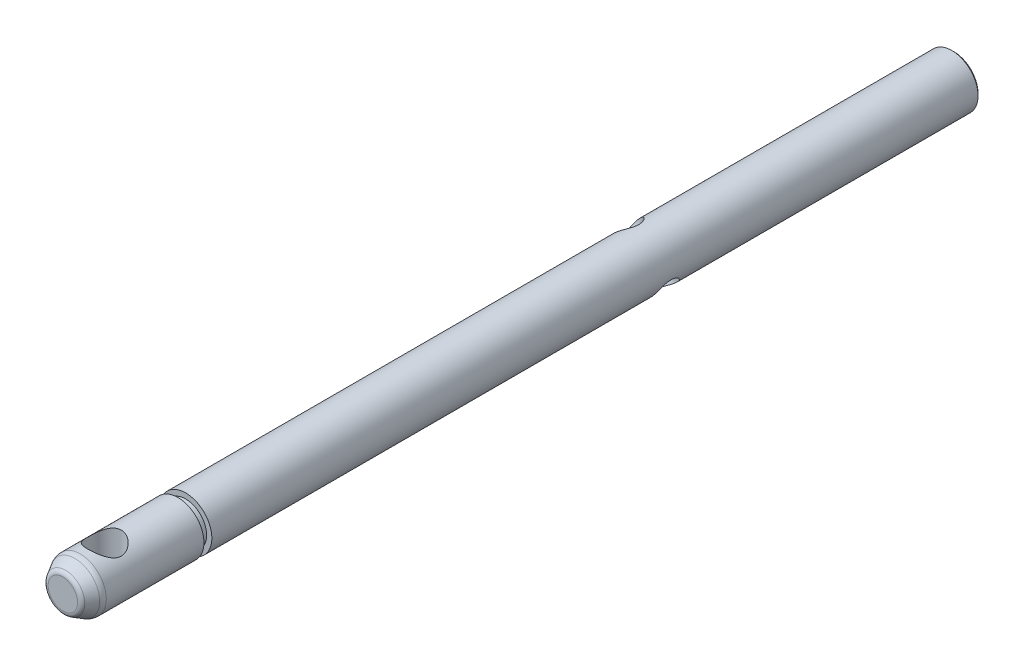
SolidWorks part; units mm, degrees
material "AISI Type 316L stainless steel"
ref_plane "Front Plane" through (0, 0, 0) normal (0, 0, 1) x (1, 0, 0)
ref_plane "Top Plane" through (0, 0, 0) normal (0, 1, 0) x (1, 0, 0)
ref_plane "Right Plane" through (0, 0, 0) normal (1, 0, 0) x (0, 0, -1)
ref_plane "Plane1" through (0, 0, 0) normal (0, -1, 0) x (1, 0, 0)
sketch "Sketch1" plane through (0, 0, 0) normal (0, -1, 0) x (1, 0, 0)
  line L0 (1.7, 11.75) -> (0, 11.75)
  line L1 (0, 11.75) -> (0, -73.5)
  line L2 (0, -73.5) -> (2.5, -73.5)
  line L3 (2.5, -73.5) -> (2.5, 0)
  line L4 (2.5, 0) -> (2, 0)
  line L5 (2, 0) -> (2, 0.75)
  line L6 (2, 0.75) -> (2.5, 0.75)
  line L7 (2.5, 0.75) -> (2.5, 10.3644)
  line L8 (2.5, 10.3644) -> (1.7, 11.75)
  line L9 (0, 11.75) -> (0, -73.5) construction
  dimension "D1" = 1.7
  dimension "D2" = 2
  dimension "D3" = 2.5
  dimension "D4" = 73.5
  dimension "D5" = 74.25
  dimension "D6" = 83.8644
  dimension "D7" = 85.25
revolve "Revolve1" add sketch "Sketch1" angle 360 about L9
hole_wizard "Ø3.0mm Dowel Hole1" positions "3DSketch1" profile "Sketch3" hole size "Ø3.0" standard "ANSI Metric"
sketch3d "3DSketch1"
  point P0 (0, -2.5, 7.75)
  point P2 (0, 0, 0)
  dimension "D1" = 81.25
sketch "Sketch3" plane through (0, -2.5, 7.75) normal (1, 0, 0) x (0, 0, -1)
  line L0 (0, 0) -> (0, 5)
  line L1 (0, 5) -> (1.5, 5)
  line L2 (1.5, 5) -> (1.5, 0)
  line L5 (1.5, 0) -> (0, 0)
  line L11 (0, -4.2992) -> (0, 10.4129) construction
  point P3 (0, 0)
  dimension "Thru Hole Dia." = 3
  dimension "Thru Hole Depth" = 5
hole_wizard "M3x0.5 Tapped Hole1" positions "Sketch5" profile "Sketch4" tap size "M3x0.5" standard "ANSI Metric"
sketch "Sketch5" plane through (0, 0, 11.75) normal (0, 0, 1) x (1, 0, 0)
  point P0 (0, 0)
sketch "Sketch4" plane through (0, 0, 11.75) normal (1, 0, 0) x (0, -1, 0)
  line L0 (0, 0) -> (0, 9.2511)
  line L1 (0, 9.2511) -> (1.25, 8.5)
  line L2 (1.25, 8.5) -> (1.25, 0.25)
  line L3 (1.25, 0.25) -> (1.5, 0)
  line L5 (1.5, 0) -> (0, 0)
  line L6 (-1.25, 0.25) -> (-1.5, 0) construction
  line L10 (0, 9.2511) -> (-1.25, 8.5) construction
  line L11 (0, -6.35) -> (0, 107.95) construction
  dimension "Tap Drill Dia." = 2.5
  dimension "Tap Drill Depth" = 8.5
  dimension "Near C'Sink Dia." = 3
  dimension "Near C'Sink Angle" = 90
  dimension "Drill Angle" = 118
hole_wizard "1/8 (0.125) Clearance Dowel Hole1" positions "3DSketch3" profile "Sketch14" hole size "1/8" standard "ANSI Inch" end condition through all
sketch3d "3DSketch3"
  point P0 (0, -2.5, 7.75)
  point P3 (0, 0, 0)
  dimension "D1" = 81.25
sketch "Sketch14" plane through (0, -2.5, 7.75) normal (1, 0, 0) x (0, 0, -1)
  line L0 (0, 0) -> (0, 5)
  line L1 (0, 5) -> (1.5875, 5)
  line L2 (1.5875, 5) -> (1.5875, 0)
  line L5 (1.5875, 0) -> (0, 0)
  line L11 (0, -6.35) -> (0, 8.1084) construction
  point P3 (0, 8.1084)
  dimension "Thru Hole Dia." = 3.175
  dimension "Thru Hole Depth" = 5
hole_wizard "M3x0.5 Tapped Hole2" positions "3DSketch2" profile "Sketch8" tap size "M3x0.5" standard "ANSI Metric" end condition through all
sketch3d "3DSketch2"
  point P0 (-1.7678, 1.7678, -44)
sketch "Sketch8" plane through (-1.7678, 1.7678, -44) normal (0, 0, 1) x (-0.7071, -0.7071, 0)
  line L0 (0, 0) -> (0, 6.0355)
  line L1 (0, 6.0355) -> (1.25, 6.0355)
  line L2 (1.25, 6.0355) -> (1.25, 0)
  line L5 (1.25, 0) -> (0, 0)
  line L11 (0, -6.35) -> (0, 107.95) construction
  dimension "Thread Major Dia." = 2.5
  dimension "Thru Tap Drill Depth" = 6.0355
hole_wizard "M3x0.5 Tapped Hole3" positions "Sketch10" profile "Sketch9" tap size "M3x0.5" standard "ANSI Metric"
sketch "Sketch10" plane through (0, 0, -73.5) normal (0, 0, -1) x (-1, 0, 0)
  point P0 (0, 0)
sketch "Sketch9" plane through (0, 0, -73.5) normal (1, 0, 0) x (0, 1, 0)
  line L0 (0, 0) -> (0, 8.2511)
  line L1 (0, 8.2511) -> (1.25, 7.5)
  line L2 (1.25, 7.5) -> (1.25, 0.25)
  line L3 (1.25, 0.25) -> (1.5, 0)
  line L5 (1.5, 0) -> (0, 0)
  line L6 (-1.25, 0.25) -> (-1.5, 0) construction
  line L10 (0, 8.2511) -> (-1.25, 7.5) construction
  line L11 (0, -6.35) -> (0, 107.95) construction
  dimension "Tap Drill Dia." = 2.5
  dimension "Tap Drill Depth" = 7.5
  dimension "Near C'Sink Dia." = 3
  dimension "Near C'Sink Angle" = 90
  dimension "Drill Angle" = 118
chamfer "Chamfer1" distance 0.2 angle 45 1 edges at (-2.5, 0, -73.5)
fillet "Fillet1" radius 1 1 edges at (-2.5, 0, 10.3644)
fillet "Fillet2" radius 0.5 1 edges at (-1.7, 0, 11.75)
